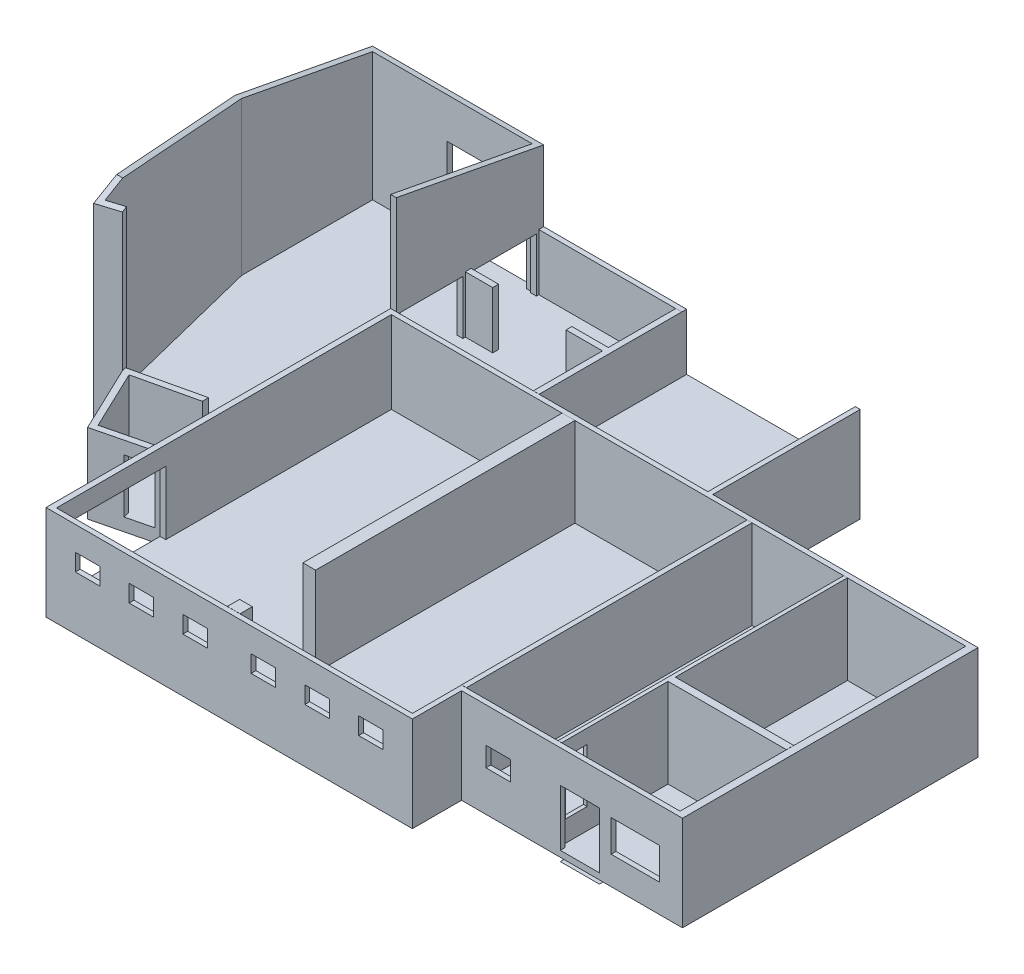
SolidWorks part; units mm, degrees
ref_plane "Ebene vorne" through (0, 0, 0) normal (0, 0, 1) x (1, 0, 0)
ref_plane "Ebene oben" through (0, 0, 0) normal (0, 1, 0) x (1, 0, 0)
ref_plane "Ebene rechts" through (0, 0, 0) normal (1, 0, 0) x (0, 0, -1)
sketch "Skizze1" plane through (0, 0, 0) normal (0, 1, 0) x (1, 0, 0)
  line L0 (14990, -18120) -> (14990, -20130)
  line L1 (0, 0) -> (13180, 0)
  line L4 (24030, -6030) -> (24030, -18120)
  line L5 (13180, 0) -> (13180, -6030)
  line L6 (13180, -6030) -> (24030, -6030)
  line L7 (14990, -20130) -> (0, -20130)
  line L8 (0, -20130) -> (0, 0)
  line L9 (14990, -18120) -> (24030, -18120)
  point P0 (0, 0)
  dimension "D1" = 14990
  dimension "D2" = 20130
  dimension "D3" = 9040
  dimension "D4" = 2010
  dimension "D5" = 13180
  dimension "D6" = 6030
extrude "Aufsatz-Linear austragen4" add sketch "Skizze1" along normal blind 250
sketch "Skizze5" plane through (0, 250, 0) normal (0, 1, 0) x (1, 0, 0)
  line L0 (23730, -6230) -> (23730, -17920)
  line L1 (23730, -17920) -> (14790, -17920)
  line L2 (14790, -17920) -> (14790, -19930)
  line L3 (14790, -19930) -> (230, -19930)
  line L4 (230, -19930) -> (230, -6230)
  line L5 (230, -200) -> (12980, -200)
  line L6 (12980, -200) -> (12980, -6030)
  line L7 (230, -6230) -> (23730, -6230)
  line L8 (24030, -18120) -> (24030, -6030) construction
  line L9 (14990, -18120) -> (24030, -18120) construction
  line L10 (14990, -20130) -> (14990, -18120) construction
  line L11 (0, -20130) -> (14990, -20130) construction
  line L12 (0, 0) -> (0, -20130) construction
  line L13 (13180, 0) -> (0, 0) construction
  line L14 (13180, -6030) -> (13180, 0) construction
  line L15 (24030, -6030) -> (13180, -6030) construction
  line L16 (0, -20130) -> (14990, -20130)
  line L17 (14990, -20130) -> (14990, -18120)
  line L18 (14990, -18120) -> (24030, -18120)
  line L19 (24030, -18120) -> (24030, -6030)
  line L20 (24030, -6030) -> (13180, -6030)
  line L21 (13180, -6030) -> (13180, 0)
  line L22 (13180, 0) -> (0, 0)
  line L23 (0, 0) -> (0, -20130)
  line L24 (12980, -6030) -> (230, -6030)
  line L25 (230, -6030) -> (230, -200)
  dimension "D1" = 300
  dimension "D2" = 200
  dimension "D3" = 200
  dimension "D4" = 200
  dimension "D5" = 230
  dimension "D6" = 200
  dimension "D7" = 200
  dimension "D8" = 200
extrude "Aufsatz-Linear austragen5" add sketch "Skizze5" along normal blind 3635
sketch "Skizze6" plane through (0, 250, 0) normal (0, 1, 0) x (1, 0, 0)
  line L0 (18890, -17920) -> (18890, -13570)
  line L1 (14790, -17920) -> (23730, -17920) construction
  line L2 (23730, -6230) -> (230, -6230) construction
  line L3 (18890, -6230) -> (18740, -6230)
  line L4 (23730, -6230) -> (230, -6230) construction
  line L5 (18740, -6230) -> (18740, -17920)
  line L6 (18740, -17920) -> (18890, -17920)
  line L7 (23730, -17920) -> (23730, -6230) construction
  line L8 (23730, -17920) -> (23730, -6230) construction
  line L9 (18890, -13270) -> (23730, -13270)
  line L11 (18890, -13570) -> (23730, -13570)
  line L12 (23730, -13270) -> (23730, -13570)
  line L13 (18890, -13270) -> (18890, -6230)
  line L14 (14990, -20130) -> (14990, -18120) construction
  line L15 (14790, -17920) -> (14990, -17920)
  line L16 (14790, -17920) -> (14790, -6230)
  line L17 (14790, -6230) -> (14990, -6230)
  line L18 (14990, -17920) -> (14990, -6230)
  line L19 (12980, -200) -> (230, -200) construction
  line L20 (5840, -200) -> (6080, -200)
  line L21 (5840, -200) -> (5840, -2965)
  line L22 (5840, -6030) -> (6080, -6030)
  line L23 (6080, -200) -> (6080, -6030)
  line L24 (230, -6030) -> (12980, -6030) construction
  line L25 (12980, -6030) -> (12980, -200) construction
  line L26 (23730, -6230) -> (230, -6230) construction
  line L27 (7220, -6230) -> (7740, -6230)
  line L28 (7220, -6230) -> (7220, -16840)
  line L29 (7220, -16840) -> (7740, -16840)
  line L30 (7740, -6230) -> (7740, -16840)
  line L31 (230, -19930) -> (14790, -19930) construction
  line L32 (7220, -19430) -> (7740, -19430)
  line L33 (7220, -19430) -> (7220, -19930)
  line L34 (7220, -19930) -> (7740, -19930)
  line L35 (7740, -19430) -> (7740, -19930)
  line L36 (230, -200) -> (230, -6030) construction
  line L37 (230, -2965) -> (1350, -2965)
  line L38 (230, -2965) -> (230, -3205)
  line L39 (230, -3205) -> (1350, -3205)
  line L40 (1350, -2965) -> (1350, -3205)
  line L41 (12980, -200) -> (230, -200) construction
  line L42 (4350, -2965) -> (5840, -2965)
  line L43 (4350, -2965) -> (4350, -3205)
  line L44 (4350, -3205) -> (5840, -3205)
  line L46 (5840, -3205) -> (5840, -6030)
  dimension "D1" = 150
  dimension "D2" = 4840
  dimension "D3" = 4350
  dimension "D4" = 300
  dimension "D5" = 6900
  dimension "D6" = 240
  dimension "D7" = 520
  dimension "D8" = 7050
  dimension "D9" = 500
  dimension "D10" = 2590
  dimension "D11" = 240
  dimension "D12" = 1120
  dimension "D13" = 3000
  dimension "D14" = 2765
extrude "Aufsatz-Linear austragen6" add sketch "Skizze6" along normal blind 3640
sketch "Skizze7" plane through (0, 0, 18120) normal (0, 0, 1) x (1, 0, 0)
  line L0 (24030, 3885) -> (24030, 0) construction
  line L1 (21110, 2450) -> (23090, 2450)
  line L2 (21110, 2450) -> (21110, 1150)
  line L3 (21110, 1150) -> (23090, 1150)
  line L4 (23090, 2450) -> (23090, 1150)
  line L5 (14990, 0) -> (24030, 0) construction
  line L7 (19030, 2550) -> (20630, 2550)
  line L8 (19030, 2550) -> (19030, 250)
  line L9 (19030, 250) -> (20630, 250)
  line L10 (20630, 2550) -> (20630, 250)
  line L11 (15990, 2450) -> (16990, 2450)
  line L12 (15990, 2450) -> (15990, 1650)
  line L13 (15990, 1650) -> (16990, 1650)
  line L14 (16990, 2450) -> (16990, 1650)
  dimension "D1" = 1980
  dimension "D2" = 940
  dimension "D3" = 1150
  dimension "D4" = 2450
  dimension "D5" = 3400
  dimension "D6" = 1600
  dimension "D7" = 250
  dimension "D8" = 2300
  dimension "D9" = 1000
  dimension "D10" = 7040
  dimension "D11" = 800
extrude "Schnitt-Linear austragen1" cut sketch "Skizze7" against normal up to next
sketch "Skizze8" plane through (18890, 0, 0) normal (1, 0, 0) x (0, 0, -1)
  line L0 (-17920, 3885) -> (-17920, 250) construction
  line L1 (-17770, 3310) -> (-16880, 3310)
  line L2 (-17770, 3310) -> (-17770, 1110)
  line L3 (-17770, 1110) -> (-16880, 1110)
  line L4 (-16880, 3310) -> (-16880, 1110)
  line L5 (-17920, 250) -> (-13570, 250) construction
  dimension "D1" = 150
  dimension "D2" = 890
  dimension "D3" = 860
  dimension "D4" = 2200
extrude "Schnitt-Linear austragen2" cut sketch "Skizze8" against normal up to next
sketch "Skizze9" plane through (0, 0, 0) normal (-1, 0, 0) x (0, 0, 1)
  line L0 (0, 0) -> (20130, 0) construction
  line L1 (15460, 3125) -> (19330, 3125)
  line L2 (15460, 3125) -> (15460, 525)
  line L3 (15460, 525) -> (19330, 525)
  line L4 (19330, 3125) -> (19330, 525)
  line L5 (20130, 3885) -> (20130, 0) construction
  line L6 (0, 3885) -> (0, 0) construction
  line L7 (300, 3775) -> (2865, 3775)
  line L8 (300, 3775) -> (300, 1575)
  line L9 (300, 1575) -> (2865, 1575)
  line L10 (2865, 3775) -> (2865, 1575)
  line L11 (3305, 3775) -> (5870, 3775)
  line L12 (3305, 3775) -> (3305, 1575)
  line L13 (3305, 1575) -> (5870, 1575)
  line L14 (5870, 3775) -> (5870, 1575)
  dimension "D1" = 525
  dimension "D2" = 800
  dimension "D3" = 3870
  dimension "D4" = 2600
  dimension "D5" = 1575
  dimension "D6" = 2565
  dimension "D7" = 300
  dimension "D8" = 440
  dimension "D9" = 2200
extrude "Schnitt-Linear austragen3" cut sketch "Skizze9" against normal up to next
sketch "Skizze10" plane through (0, 250, 0) normal (0, 1, 0) x (1, 0, 0)
  line L8 (0, -20130) -> (14990, -20130) construction
  line L9 (0, -14902.5027) -> (0, -15160)
  line L26 (0, -15160) -> (-2621.3867, -15806.7858)
  line L27 (-2621.3867, -15806.7858) -> (-3994.9173, -12922.2993)
  line L28 (0, -12000) -> (-3994.9173, -12922.2993)
  line L29 (0, -14902.5027) -> (-2483.3257, -15515.2241)
  line L30 (-2483.3257, -15515.2241) -> (-3635.3713, -13095.8676)
  line L31 (0, -12256.576) -> (-3635.3713, -13095.8676)
  line L32 (-59.8876, -14917.279) -> (-2483.3257, -15515.2241) construction
  line L34 (56.2378, -12243.5925) -> (-3635.3713, -13095.8676) construction
  line L37 (0, -12000) -> (0, -12256.576)
  dimension "D2" = 2483.3257
  dimension "D3" = 2621.3867
  dimension "D4" = 4970
  dimension "D11" = 4100
  dimension "D12" = 2700
  dimension "D13" = 3160
  dimension "D15" = 250
extrude "Aufsatz-Linear austragen7" add sketch "Skizze10" along normal blind 3000
sketch "Skizze11" plane through (0, 250, 0) normal (0, 1, 0) x (1, 0, 0)
  line L1 (230, -6230) -> (7220, -6230)
  line L2 (230, -6230) -> (230, -19930)
  line L3 (230, -19930) -> (7220, -19930)
  line L4 (7220, -6230) -> (7220, -19930)
extrude "Aufsatz-Linear austragen8" add sketch "Skizze11" along normal blind 275
sketch "Skizze12" plane through (0, 250, 0) normal (0, 1, 0) x (1, 0, 0)
  line L0 (12980, -6030) -> (12980, -200) construction
  line L1 (230, -200) -> (12980, -200)
  line L2 (230, -200) -> (230, -6030)
  line L3 (230, -6030) -> (12980, -6030)
  line L4 (12980, -200) -> (12980, -6030)
extrude "Aufsatz-Linear austragen9" add sketch "Skizze12" along normal blind 1325
sketch "Skizze13" plane through (0, 0, 19930) normal (0, 0, -1) x (-1, 0, 0)
  line L0 (-4895, 525) -> (-10130, 250)
  line L1 (-230, 525) -> (-7220, 525) construction
  line L2 (-7740, 250) -> (-14790, 250) construction
  line L3 (-230, 3885) -> (-230, 525) construction
  line L4 (-4895, 525) -> (-4895, 250)
  line L5 (-4895, 250) -> (-10130, 250)
  dimension "D1" = 4665
  dimension "D2" = 9900
extrude "Aufsatz-Linear austragen10" add sketch "Skizze13" along normal up to surface (3090 mm away) up to face at (7428, 1761, 16840)
sketch "Skizze14" plane through (0, 0, 19930) normal (0, 0, -1) x (-1, 0, 0)
  line L0 (-4895, 525) -> (-10130, 250) construction
  line L1 (-230, 525) -> (-7220, 525) construction
  line L2 (-230, 3885) -> (-230, 525) construction
  line L3 (-4895, 525) -> (-7220, 525)
  line L4 (-7220, 525) -> (-7220, 402.8653)
  line L5 (-7220, 402.8653) -> (-4895, 525)
  dimension "D1" = 4665
extrude "Schnitt-Linear austragen4" cut sketch "Skizze14" along normal up to surface (3090 mm away) up to face at (7428, 1816.6829, 16840)
sketch "Skizze18" plane through (0, 1575, 0) normal (0, 1, 0) x (1, 0, 0)
  line L0 (0, 0) -> (-6770, 0)
  line L1 (-6770, 0) -> (-6770, -5625)
  line L2 (-6770, -5625) -> (-4848.6563, -13331.0887)
  line L3 (-4848.6563, -13331.0887) -> (-3911.5215, -13097.4347)
  line L4 (-3994.9173, -12922.2993) -> (-2621.3867, -15806.7858) construction
  line L5 (0, -240) -> (-6530, -240)
  line L6 (-6530, -240) -> (-6530, -5595.5317)
  line L7 (-6530, -5595.5317) -> (-4673.8466, -13040.1564)
  line L8 (-4673.8466, -13040.1564) -> (-3969.5828, -12864.5637)
  line L9 (0, 0) -> (0, -240)
  line L10 (-3911.5215, -13097.4347) -> (-3969.5828, -12864.5637)
  dimension "D1" = 6770
  dimension "D2" = 5625
  dimension "D3" = 166
  dimension "D4" = 7942
  dimension "D5" = 240
extrude "Aufsatz-Linear austragen12" add sketch "Skizze18" along normal blind 8000
sketch "Skizze19" plane through (0, 1575, 0) normal (0, -1, 0) x (1, 0, 0)
  line L0 (-2621.3867, 15806.7858) -> (0, 15160) construction
  line L1 (-3994.9173, 12922.2993) -> (-2621.3867, 15806.7858) construction
  line L2 (0, 0) -> (0, 20130) construction
  line L3 (0, 0) -> (-6770, 0) construction
  line L4 (-6770, 0) -> (-6770, 5625) construction
  line L5 (-6770, 5625) -> (-4848.6563, 13331.0887) construction
  line L6 (-4848.6563, 13331.0887) -> (-3911.5215, 13097.4347) construction
  line L7 (-2621.3867, 15806.7858) -> (0, 15160)
  line L8 (-3911.5215, 13097.4347) -> (-2621.3867, 15806.7858)
  line L9 (0, 0) -> (0, 15160)
  line L10 (0, 0) -> (-6770, 0)
  line L11 (-6770, 0) -> (-6770, 5625)
  line L12 (-6770, 5625) -> (-4848.6563, 13331.0887)
  line L13 (-4848.6563, 13331.0887) -> (-3911.5215, 13097.4347)
extrude "Aufsatz-Linear austragen13" add sketch "Skizze19" along normal up to surface (1575 mm away) up to face at (13050, 0, 11070)
sketch "Skizze20" plane through (23790, 0, 0) normal (-1, 0, 0) x (0, 0, 1)
  line L0 (6030, 3885) -> (18120, 3885) construction
  line L1 (12075, 3885) -> (12075, 53885) construction
  line L2 (12075, 9126.8586) -> (-1495.4792, 6548.4986) construction
  line L3 (5607.5, 10355) -> (16555, 8276.1322) construction
  line L4 (12075, 9126.8586) -> (21774.9238, 7284.8984) construction
  line L5 (-5340, 8275) -> (5607.5, 10355) construction
  line L6 (12075.0025, 9075.9647) -> (-1187.358, 6556.1464)
  line L7 (12075.0025, 9075.9647) -> (21923.9238, 7205.7107)
  line L8 (12075, 9126.8586) -> (18876.5778, 7835.2778) construction
  line L9 (12075.0025, 9075.9647) -> (18867.2498, 7786.1556) construction
  line L10 (21923.9238, 7205.7107) -> (21923.9238, 13266.9089)
  line L11 (21923.9238, 13266.9089) -> (-1198.8091, 13266.9089)
  line L12 (-1198.8091, 13266.9089) -> (-1187.358, 6556.1464)
  line L13 (12075, 9126.8586) -> (-1196.6909, 6605.2677) construction
  point P6 (12075, 3885)
  dimension "D1" = 50
extrude "Schnitt-Linear austragen8" cut sketch "Skizze20" against normal through all both and the other way through all
sketch "Skizze21" plane through (0, 3885, 0) normal (0, 1, 0) x (1, 0, 0)
  line L0 (230, -3205) -> (230, -6030) construction
  line L1 (0, 0) -> (230, 0)
  line L2 (0, 0) -> (0, -6030)
  line L3 (0, -6030) -> (230, -6030)
  line L4 (230, 0) -> (230, -6030)
  dimension "D1" = 6030
extrude "Aufsatz-Linear austragen14" add sketch "Skizze21" along normal up to surface (2896.7417 mm away)
ref_plane "Ebene1" through (-1200, 0, 0) normal (-1, 0, 0) x (0, 0, 1)
sketch "Skizze22" plane through (-1200, 0, 0) normal (-1, 0, 0) x (0, 0, 1)
  line L0 (9555.4096, 1575) -> (9815.4096, 1575)
  line L1 (5870, 1575) -> (12000, 1575) construction
  line L2 (9815.4096, 1575) -> (9815.4096, 1395)
  line L3 (9815.4096, 1395) -> (10075.4096, 1395)
  line L4 (10075.4096, 1395) -> (10075.4096, 1215)
  line L5 (10075.4096, 1215) -> (10335.4096, 1215)
  line L6 (10335.4096, 1215) -> (10335.4096, 1035)
  line L7 (10335.4096, 1035) -> (10595.4096, 1035)
  line L8 (10595.4096, 1035) -> (10595.4096, 855)
  line L9 (10595.4096, 855) -> (10855.4096, 855)
  line L10 (10855.4096, 855) -> (10855.4096, 675)
  line L12 (10855.4096, 675) -> (13323.1605, 675)
  line L13 (13323.1605, 675) -> (13323.1605, 5461.3971)
  line L14 (13323.1605, 5461.3971) -> (9555.4096, 5461.3971)
  line L15 (9555.4096, 5461.3971) -> (9555.4096, 1575)
  dimension "D1" = 260
  dimension "D2" = 180
extrude "Schnitt-Linear austragen9" cut sketch "Skizze22" against normal up to surface (1200 mm away) up to face at (0, 1825, 17395)
sketch "Skizze23" plane through (0, 1575, 0) normal (0, 1, 0) x (1, 0, 0)
  line L6 (-1200, -13323.1605) -> (-1200, -12533.6179)
  line L7 (-1200, -12533.6179) -> (-3635.3713, -13095.8676)
  line L8 (-3635.3713, -13095.8676) -> (-2483.3257, -15515.2241)
  line L9 (-2483.3257, -15515.2241) -> (0, -14902.5027)
  line L10 (0, -14902.5027) -> (0, -13323.1605)
  line L11 (0, -13323.1605) -> (-1200, -13323.1605)
  line L12 (-1200, -13323.1605) -> (-1200, -12533.6179)
  line L13 (-1200, -12533.6179) -> (-3635.3713, -13095.8676)
  line L14 (-3635.3713, -13095.8676) -> (-2483.3257, -15515.2241)
  line L15 (-2483.3257, -15515.2241) -> (0, -14902.5027)
  line L16 (0, -14902.5027) -> (0, -13323.1605)
  line L17 (0, -13323.1605) -> (-1200, -13323.1605)
  dimension "D1" = 0
extrude "Schnitt-Linear austragen10" cut sketch "Skizze23" against normal up to surface (1050 mm away) up to face at (2515, 525, 15558)
sketch "Skizze24" plane through (3525.8452, 0, 14290.0533) normal (0.2396, 0, 0.9709) x (0.9709, 0, -0.2396)
  line L0 (-3631.5825, 3250) -> (-3631.5825, 0) construction
  line L1 (-5101.5825, 2725) -> (-4061.5825, 2725)
  line L2 (-5101.5825, 2725) -> (-5101.5825, 525)
  line L3 (-5101.5825, 525) -> (-4061.5825, 525)
  line L4 (-4061.5825, 2725) -> (-4061.5825, 525)
  line L5 (-3703.4476, 525) -> (-4630.5072, 525) construction
  dimension "D1" = 1040
  dimension "D2" = 430
  dimension "D3" = 2200
extrude "Schnitt-Linear austragen11" cut sketch "Skizze24" against normal blind 300
sketch "Skizze25" plane through (0, 0, 20130) normal (0, 0, 1) x (1, 0, 0)
  line L0 (0, 0) -> (14990, 0) construction
  line L1 (1200, 2900) -> (2200, 2900)
  line L2 (1200, 2900) -> (1200, 2200)
  line L3 (1200, 2200) -> (2200, 2200)
  line L4 (2200, 2900) -> (2200, 2200)
  line L5 (3400, 2900) -> (4400, 2900)
  line L6 (3400, 2900) -> (3400, 2200)
  line L7 (3400, 2200) -> (4400, 2200)
  line L8 (4400, 2900) -> (4400, 2200)
  line L9 (5600, 2900) -> (6600, 2900)
  line L10 (5600, 2900) -> (5600, 2200)
  line L11 (5600, 2200) -> (6600, 2200)
  line L12 (6600, 2900) -> (6600, 2200)
  line L13 (8390, 2900) -> (9390, 2900)
  line L14 (8390, 2900) -> (8390, 2200)
  line L15 (8390, 2200) -> (9390, 2200)
  line L16 (9390, 2900) -> (9390, 2200)
  line L17 (10590, 2900) -> (11590, 2900)
  line L18 (10590, 2900) -> (10590, 2200)
  line L19 (10590, 2200) -> (11590, 2200)
  line L20 (11590, 2900) -> (11590, 2200)
  line L21 (12790, 2900) -> (13790, 2900)
  line L22 (12790, 2900) -> (12790, 2200)
  line L23 (12790, 2200) -> (13790, 2200)
  line L24 (13790, 2900) -> (13790, 2200)
  line L25 (230, 3885) -> (230, 525) construction
  line L26 (14790, 3885) -> (14790, 250) construction
  dimension "D1" = 1000
  dimension "D2" = 700
  dimension "D3" = 2200
  dimension "D4" = 1200
  dimension "D5" = 970
  dimension "D6" = 1200
  dimension "D7" = 1000
  dimension "D8" = 1200
  dimension "D9" = 1200
extrude "Schnitt-Linear austragen12" cut sketch "Skizze25" against normal up to next
sketch "Skizze26" plane through (0, 0, 200) normal (0, 0, 1) x (1, 0, 0)
  line L0 (12980, 3885) -> (12980, 1575) construction
  line L1 (6080, 1575) -> (12980, 1575)
  line L2 (6080, 1575) -> (6080, 5392.7447)
  line L3 (6080, 5392.7447) -> (12980, 5392.7447)
  line L4 (12980, 1575) -> (12980, 5392.7447)
extrude "Schnitt-Linear austragen13" cut sketch "Skizze26" against normal up to next
sketch "Skizze27" plane through (0, 0, 240) normal (0, 0, 1) x (1, 0, 0)
  line L0 (-6530, 1575) -> (0, 1575) construction
  line L1 (-3490, 5175) -> (-240, 5175)
  line L2 (-3490, 5175) -> (-3490, 1575)
  line L3 (-3490, 1575) -> (-240, 1575)
  line L4 (-240, 5175) -> (-240, 1575)
  line L5 (0, 6827.3412) -> (0, 1575) construction
  dimension "D1" = 3250
  dimension "D2" = 240
  dimension "D3" = 3600
extrude "Schnitt-Linear austragen14" cut sketch "Skizze27" against normal up to next
surface "Oberfläche-Offset1" parameters "D1"=400
